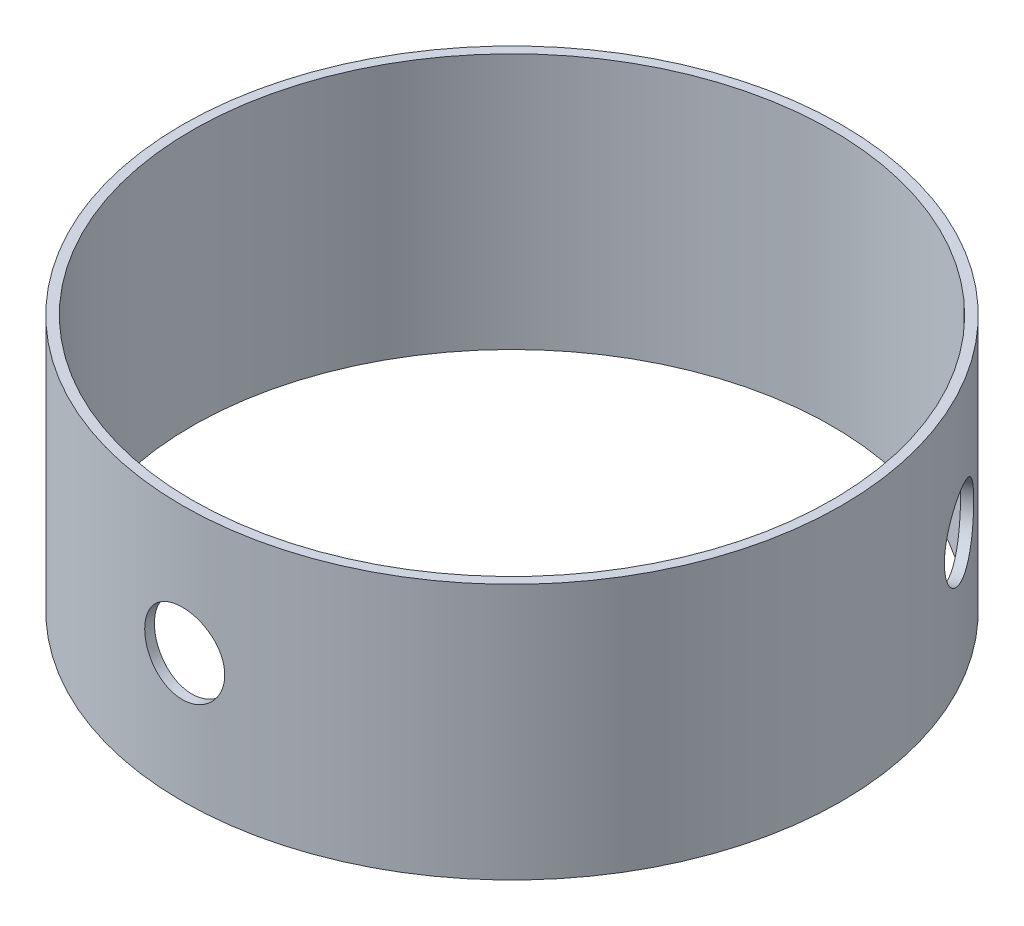
SolidWorks part; units mm, degrees
ref_plane "Front Plane" through (0, 0, 0) normal (0, 0, 1) x (1, 0, 0)
ref_plane "Top Plane" through (0, 0, 0) normal (0, 1, 0) x (1, 0, 0)
ref_plane "Right Plane" through (0, 0, 0) normal (1, 0, 0) x (0, 0, -1)
sketch "Sketch1" plane through (0, 0, 0) normal (0, 1, 0) x (1, 0, 0)
  circle A0 centre (0, 0) radius 65.405
  circle A1 centre (0, 0) radius 63.5
  dimension "D1" = 130.81
  dimension "D2" = 127
extrude "Boss-Extrude1" add sketch "Sketch1" along normal mid plane 50.8
ref_plane "Plane1" through (0, 0, 65.405) normal (0, 0, 1) x (1, 0, 0)
ref_plane "Plane2" through (56.6424, 0, -32.7025) normal (0.866, 0, -0.5) x (0, -1, 0)
hole_wizard "5/8 (0.625) Diameter Hole1" positions "Sketch2" profile "Sketch3" hole size "5/8" standard "ANSI Inch"
sketch "Sketch2" plane through (56.6424, 0, -32.7025) normal (0.866, 0, -0.5) x (0, -1, 0)
  point P0 (0, 0)
  point P3 (0, 0)
sketch "Sketch3" plane through (56.6424, 0, -32.7025) normal (0, 1, 0) x (-0.5, 0, -0.866)
  line L0 (0, 0) -> (0, 3.81)
  line L1 (0, 3.81) -> (7.9375, 3.81)
  line L2 (7.9375, 3.81) -> (7.9375, 0)
  line L5 (7.9375, 0) -> (0, 0)
  line L10 (0, 3.81) -> (-7.9375, 3.81) construction
  line L11 (0, -6.35) -> (0, 107.95) construction
  dimension "Hole Dia." = 15.875
  dimension "Hole Depth" = 3.81
  dimension "Drill Angle" = 180
hole_wizard "5/8 (0.625) Diameter Hole2" positions "Sketch4" profile "Sketch5" hole size "5/8" standard "ANSI Inch"
sketch "Sketch4" plane through (0, 0, 65.405) normal (0, 0, 1) x (1, 0, 0)
  point P0 (0, 0)
sketch "Sketch5" plane through (0, 0, 65.405) normal (1, 0, 0) x (0, -1, 0)
  line L0 (0, 0) -> (0, 3.81)
  line L1 (0, 3.81) -> (7.9375, 3.81)
  line L2 (7.9375, 3.81) -> (7.9375, 0)
  line L5 (7.9375, 0) -> (0, 0)
  line L10 (0, 3.81) -> (-7.9375, 3.81) construction
  line L11 (0, -6.35) -> (0, 107.95) construction
  dimension "Hole Dia." = 15.875
  dimension "Hole Depth" = 3.81
  dimension "Drill Angle" = 180
